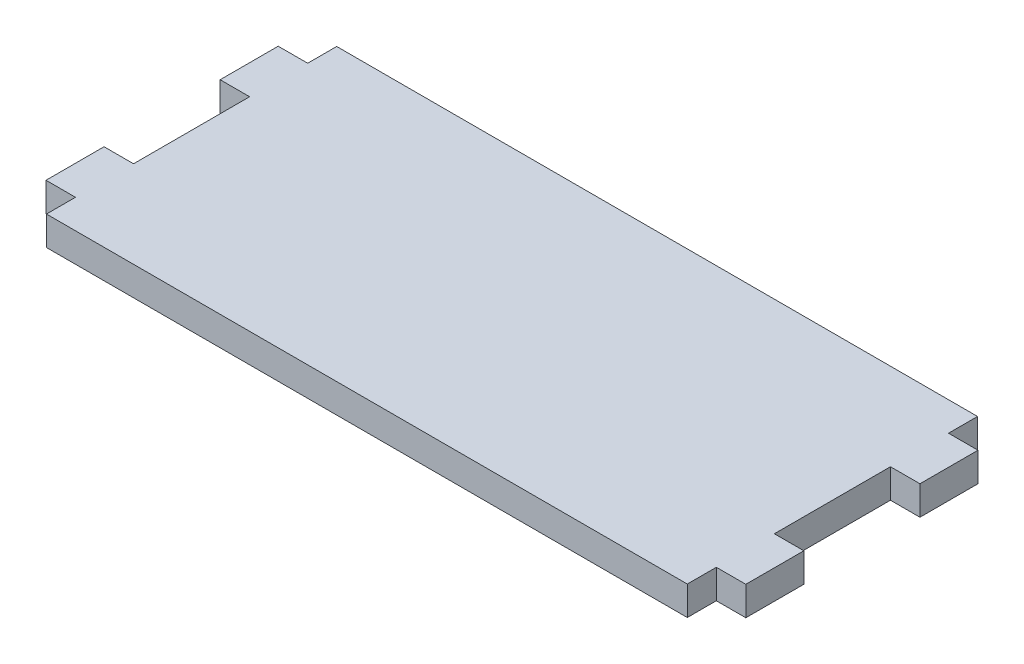
SolidWorks part; units mm, degrees
ref_plane "Front Plane" through (0, 0, 0) normal (0, 0, 1) x (1, 0, 0)
ref_plane "Top Plane" through (0, 0, 0) normal (0, 1, 0) x (1, 0, 0)
ref_plane "Right Plane" through (0, 0, 0) normal (1, 0, 0) x (0, 0, -1)
sketch "Sketch1" plane through (0, 0, 0) normal (0, 1, 0) x (1, 0, 0)
  line L1 (-35.052, -15.875) -> (35.052, -15.875)
  line L2 (-35.052, -15.875) -> (-35.052, 15.875)
  line L3 (-35.052, 15.875) -> (35.052, 15.875)
  line L4 (35.052, -15.875) -> (35.052, 15.875)
  line L5 (-35.052, -15.875) -> (35.052, 15.875) construction
  line L6 (-35.052, 15.875) -> (35.052, -15.875) construction
  point P0 (0, 0)
  dimension "D1" = 70.104
  dimension "D2" = 31.75
extrude "Boss-Extrude1" add sketch "Sketch1" along normal blind 3.175
sketch "Sketch2" plane through (0, 3.175, 0) normal (0, 1, 0) x (1, 0, 0)
  line L0 (-35.052, 12.7) -> (-38.2778, 12.7)
  line L1 (-35.052, 15.875) -> (-35.052, -15.875) construction
  line L2 (-38.2778, 12.7) -> (-38.2778, 6.35)
  line L3 (-38.2778, 6.35) -> (-35.052, 6.35)
  line L4 (-35.052, 6.35) -> (-35.052, 12.7)
  line L5 (-35.052, -6.35) -> (-38.2778, -6.35)
  line L6 (-38.2778, -6.35) -> (-38.2778, -12.7)
  line L7 (-38.2778, -12.7) -> (-35.052, -12.7)
  line L8 (-35.052, -12.7) -> (-35.052, -6.35)
  point P8 (-35.052, 0)
  point P11 (-35.052, 0)
  dimension "D1" = 3.2258
  dimension "D2" = 6.35
  dimension "D3" = 6.35
  dimension "D4" = 6.35
  dimension "D5" = 6.35
  dimension "D6" = 3.2258
extrude "tabs" add sketch "Sketch2" against normal blind 3.175
mirror "Mirror1" about plane through (0, 0, 0) normal (1, 0, 0) of "tabs"
